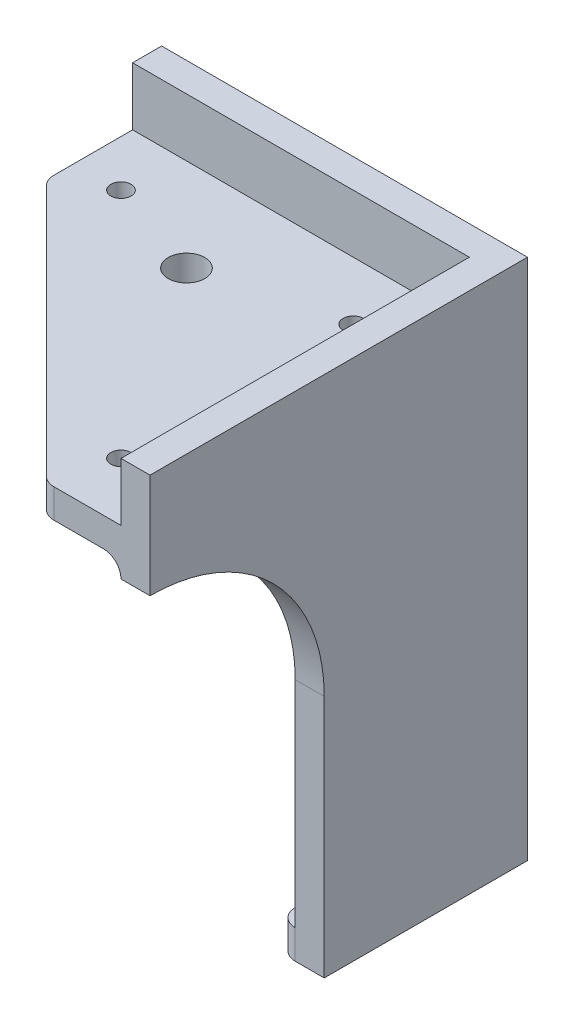
SolidWorks part; units mm, degrees
ref_plane "Alzado" through (0, 0, 0) normal (0, 0, 1) x (1, 0, 0)
ref_plane "Planta" through (0, 0, 0) normal (0, 1, 0) x (1, 0, 0)
ref_plane "Vista lateral" through (0, 0, 0) normal (1, 0, 0) x (0, 0, -1)
sketch "Croquis1" plane through (0, 0, 0) normal (0, 0, 1) x (1, 0, 0)
  line L0 (-63, 0) -> (0, 0)
  line L1 (0, 0) -> (0, -90)
  line L2 (0, -90) -> (-33, -90)
  line L3 (-33, -90) -> (-33, -48)
  line L6 (-63, -18) -> (-63, 0)
  arc A0 (-33, -48) -> (-63, -18) centre (-63, -48) ccw
  dimension "D1" = 60
  dimension "D2" = 33
  dimension "D3" = 90
  dimension "D4" = 63
  dimension "D5" = 42
extrude "Saliente-Extruir1" add sketch "Croquis1" along normal blind 5 separate body
sketch "Croquis2" plane through (0, 0, 5) normal (0, 0, 1) x (1, 0, 0)
  line L1 (0, 0) -> (-5, 0)
  line L2 (0, 0) -> (0, -90)
  line L3 (0, -90) -> (-5, -90)
  line L4 (-5, 0) -> (-5, -90)
  line L5 (0, -90) -> (0, 0) construction
  line L6 (0, 0) -> (-63, 0) construction
  line L7 (-33, -90) -> (0, -90) construction
  dimension "D1" = 5
extrude "Saliente-Extruir2" add sketch "Croquis2" along normal blind 60
sketch "Croquis3" plane through (0, 0, 0) normal (1, 0, 0) x (0, 0, -1)
  line L0 (-65, -90) -> (-35, -90)
  line L1 (-35, -90) -> (-35, -48)
  line L2 (-65, -90) -> (-65, -18)
  line L3 (-65, -90) -> (-65, 0) construction
  line L4 (-65, -90) -> (0, -90) construction
  arc A0 (-35, -48) -> (-65, -18) centre (-65, -48) ccw
  dimension "D3" = 60
  dimension "D1" = 30
  dimension "D2" = 72
extrude "Cortar-Extruir1" cut sketch "Croquis3" against normal up to surface (5 mm away) up to face at (-5, -33.75, 50)
sketch "Croquis4" plane through (0, -90, 0) normal (0, -1, 0) x (1, 0, 0)
  line L0 (-33, 8) -> (-8, 8)
  line L1 (-33, 5) -> (-5, 5)
  line L2 (-33, 5) -> (-33, 8)
  line L3 (-8, 35) -> (-5, 35)
  line L4 (-5, 5) -> (-5, 35)
  line L5 (-8, 8) -> (-8, 35)
  line L6 (-33, 5) -> (-5, 5) construction
  line L7 (-5, 35) -> (-5, 5) construction
  line L8 (-5, 35) -> (0, 35) construction
  line L9 (-33, 5) -> (-33, 0) construction
  dimension "D1" = 3
extrude "Saliente-Extruir3" add sketch "Croquis4" against normal blind 5
fillet "Redondeo1" radius 3 2 edges at (-33, -87.5, 8) (-8, -87.5, 35)
sketch "Croquis5" plane through (0, 0, 5) normal (0, 0, 1) x (1, 0, 0)
  line L0 (-5, 0) -> (-63, 0) construction
  line L1 (-5, -10) -> (-63, -10)
  line L2 (-5, -10) -> (-5, -15)
  line L3 (-5, -15) -> (-63, -15)
  line L4 (-63, -10) -> (-63, -15)
  line L6 (-63, 0) -> (-63, -18) construction
  line L7 (-5, 0) -> (-5, -85) construction
  dimension "D1" = 10
  dimension "D2" = 5
extrude "Saliente-Extruir4" add sketch "Croquis5" along normal up to surface (60 mm away) up to face at (-2.5, -9, 65)
sketch "Croquis6" plane through (0, -10, 0) normal (0, 1, 0) x (1, 0, 0)
  line L0 (-63, -19.8176) -> (-17.8176, -65)
  line L1 (-63, -65) -> (-63, -5) construction
  line L2 (-63, -65) -> (-5, -65) construction
  line L3 (-17.8176, -65) -> (-63, -65)
  line L4 (-63, -65) -> (-63, -19.8176)
  line L5 (-5, -5) -> (-63, -5) construction
  line L6 (-5, -65) -> (-5, -5) construction
  circle A0 centre (-60, -18.575) radius 3 construction
  dimension "D1" = 6
  dimension "D2" = 45
  dimension "D3" = 13.575
extrude "Cortar-Extruir2" cut sketch "Croquis6" against normal up to surface (5 mm away) up to face at (-34, -15, 35)
fillet "Redondeo2" radius 3 2 edges at (-17.8176, -12.5, 65) (-63, -12.5, 19.8176)
fillet "Redondeo3" radius 3 3 edges at (-34, -15, 5) (-5, -15, 35)
sketch "Croquis7" plane through (0, -10, 0) normal (0, 1, 0) x (1, 0, 0)
  line L0 (-5, -5) -> (-63, -5) construction
  line L1 (-5, -65) -> (-5, -5) construction
  circle A0 centre (-15, -55) radius 1.75
  circle A1 centre (-15, -15) radius 1.75
  circle A2 centre (-55, -15) radius 1.75
  circle A3 centre (-37.7443, -20.975) radius 3.15
  dimension "D1" = 3.5
  dimension "D2" = 40
  dimension "D3" = 40
  dimension "D4" = 10
  dimension "D5" = 10
  dimension "D6" = 6.3
  dimension "D7" = 15.975
  dimension "D8" = 32.7443
extrude "Cortar-Extruir3" cut sketch "Croquis7" against normal up to surface (5 mm away) up to face at (-34.2416, -15, 35.6701)
